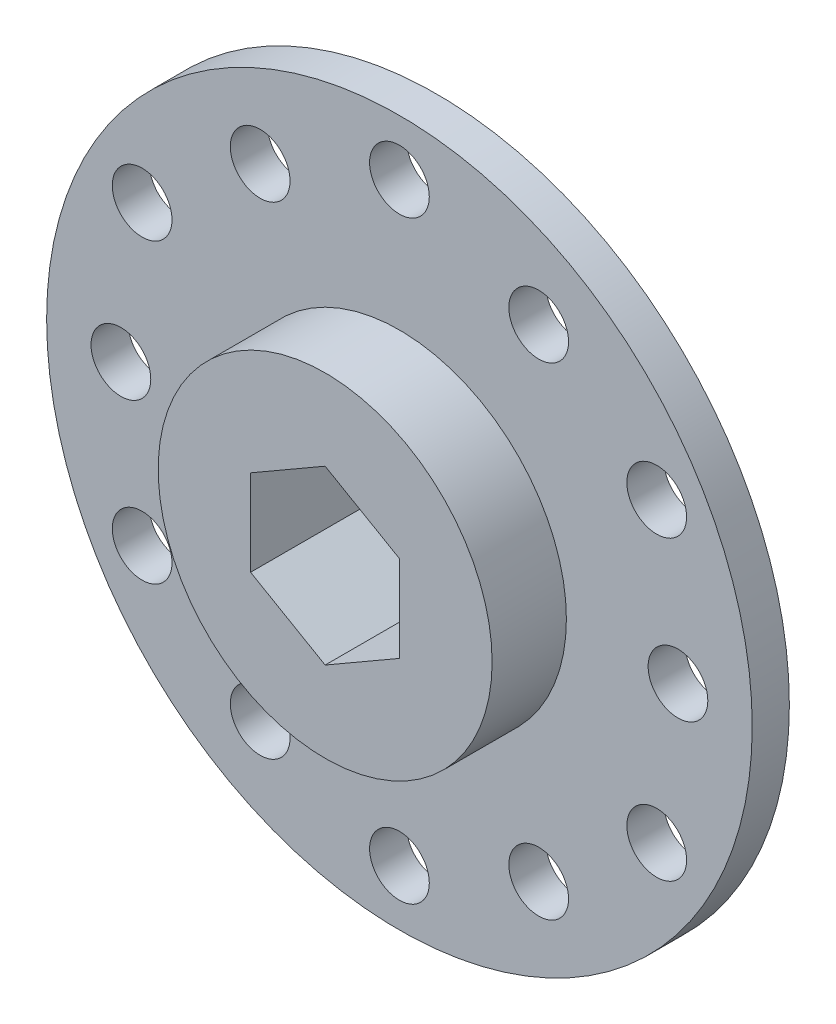
SolidWorks part; units mm, degrees
ref_plane "Front Plane" through (0, 0, 0) normal (0, 0, 1) x (1, 0, 0)
ref_plane "Top Plane" through (0, 0, 0) normal (0, 1, 0) x (1, 0, 0)
ref_plane "Right Plane" through (0, 0, 0) normal (1, 0, 0) x (0, 0, -1)
sketch "Sketch1" plane through (0, 0, 0) normal (0, 1, 0) x (1, 0, 0)
  line L0 (30.1625, 0) -> (0, 0)
  line L1 (0, 0) -> (0, -3.175)
  line L2 (0, -3.175) -> (30.1625, -3.175)
  line L3 (30.1625, -3.175) -> (30.1625, 0)
  line L4 (0, 0) -> (0, -3.175) construction
revolve "Revolve1" add sketch "Sketch1" angle 360 about L4
sketch "Sketch2" plane through (0, 0, 3.175) normal (0, 0, 1) x (1, 0, 0)
  circle A0 centre (0, 0) radius 14.2748
extrude "Boss-Extrude1" add sketch "Sketch2" along normal blind 6.35
sketch "Sketch3" plane through (0, 0, 9.525) normal (0, 0, 1) x (1, 0, 0)
  line L0 (0, -7.3617) -> (6.3754, -3.6808)
  line L1 (6.3754, -3.6808) -> (6.3754, 3.6808)
  line L2 (6.3754, 3.6808) -> (0, 7.3617)
  line L3 (0, 7.3617) -> (-6.3754, 3.6808)
  line L4 (-6.3754, 3.6808) -> (-6.3754, -3.6808)
  line L5 (-6.3754, -3.6808) -> (0, -7.3617)
extrude "Cut-Extrude1" cut sketch "Sketch3" against normal through all
hole_wizard "Hole1" positions "Sketch5" profile "Sketch4" legacy
sketch "Sketch5" plane through (0, 0, 0) normal (0, 0, -1) x (-1, 0, 0)
  point P0 (11.9062, 20.6222)
  point P1 (0, 25.4)
  point P2 (23.8125, 0)
  point P3 (21.997, 12.7)
  point P4 (11.9062, -20.6222)
  point P5 (21.997, -12.7)
  point P6 (-11.9062, -20.6222)
  point P7 (0, -25.4)
  point P8 (-23.8125, 0)
  point P9 (-21.997, -12.7)
  point P10 (-11.9062, 20.6222)
  point P11 (-21.997, 12.7)
sketch "Sketch4" plane through (-11.9062, 20.6222, 0) normal (1, 0, 0) x (0, 1, 0)
  line L0 (0, 0) -> (0, 9.525)
  line L1 (0, 9.525) -> (2.5527, 9.525)
  line L2 (2.5527, 9.525) -> (2.5527, 0)
  line L3 (2.5527, 0) -> (0, 0)
  line L4 (0, 110) -> (0, -10) construction
  dimension "Diameter" = 5.1054
  dimension "Depth" = 9.525
